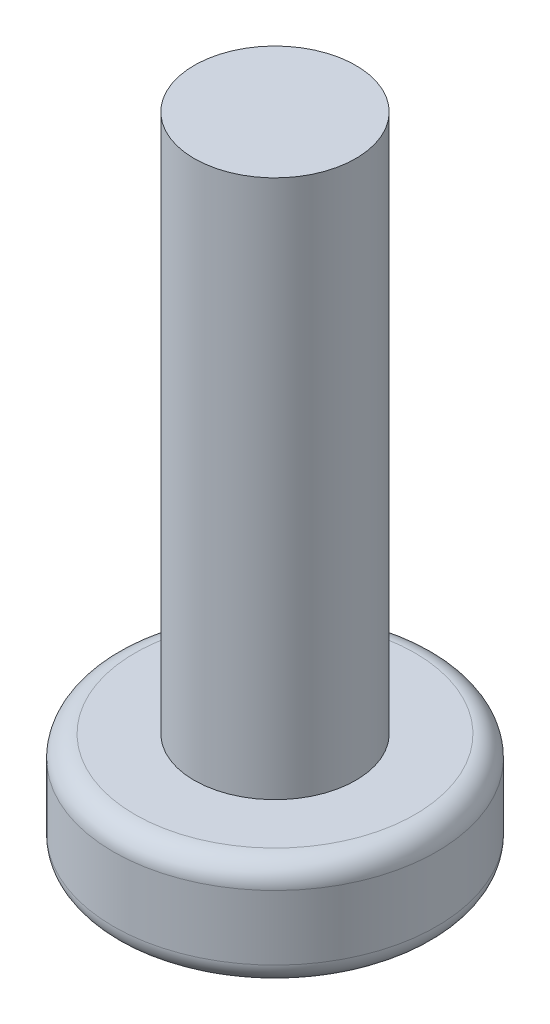
SolidWorks part; units mm, degrees
ref_plane "Front Plane" through (0, 0, 0) normal (0, 0, 1) x (1, 0, 0)
ref_plane "Top Plane" through (0, 0, 0) normal (0, 1, 0) x (1, 0, 0)
ref_plane "Right Plane" through (0, 0, 0) normal (1, 0, 0) x (0, 0, -1)
sketch "Sketch1" plane through (0, 0, 0) normal (0, 1, 0) x (1, 0, 0)
  circle A0 centre (0, 0) radius 3
  dimension "D1" = 6
extrude "Boss-Extrude1" add sketch "Sketch1" along normal blind 2
sketch "Sketch2" plane through (0, 2, 0) normal (0, 1, 0) x (1, 0, 0)
  circle A0 centre (0, 0) radius 1.5
  dimension "D1" = 3
extrude "Boss-Extrude2" add sketch "Sketch2" along normal blind 10
sketch "Sketch3" plane through (0, 0, 0) normal (0, -1, 0) x (-1, 0, 0)
  line L1 (0.45, -1.5) -> (-0.45, -1.5)
  line L2 (0.45, -1.5) -> (0.45, 1.5)
  line L3 (0.45, 1.5) -> (-0.45, 1.5)
  line L4 (-0.45, -1.5) -> (-0.45, 1.5)
  line L5 (1.5, -0.45) -> (-1.5, -0.45)
  line L6 (1.5, -0.45) -> (1.5, 0.45)
  line L7 (1.5, 0.45) -> (-1.5, 0.45)
  line L8 (-1.5, -0.45) -> (-1.5, 0.45)
  point P4 (0, -1.5)
  point P5 (0, 1.5)
  point P14 (1.5, 0)
  point P15 (-1.5, 0)
  dimension "D1" = 1.5
  dimension "D2" = 1.5
  dimension "D3" = 0.9
  dimension "D4" = 0.9
  dimension "D5" = 1.5
  dimension "D6" = 1.5
extrude "Cut-Extrude1" cut sketch "Sketch3" against normal blind 1.9 contours L2 L7 L4 L5 | L6 L7 L2 L5 | L2 L5 L4 L1 | L8 L5 L4 L7 | L7 L2 L3 L4
fillet "Fillet1" radius 0.4 2 edges at (0, 2, 3) (0, 0, 3)
